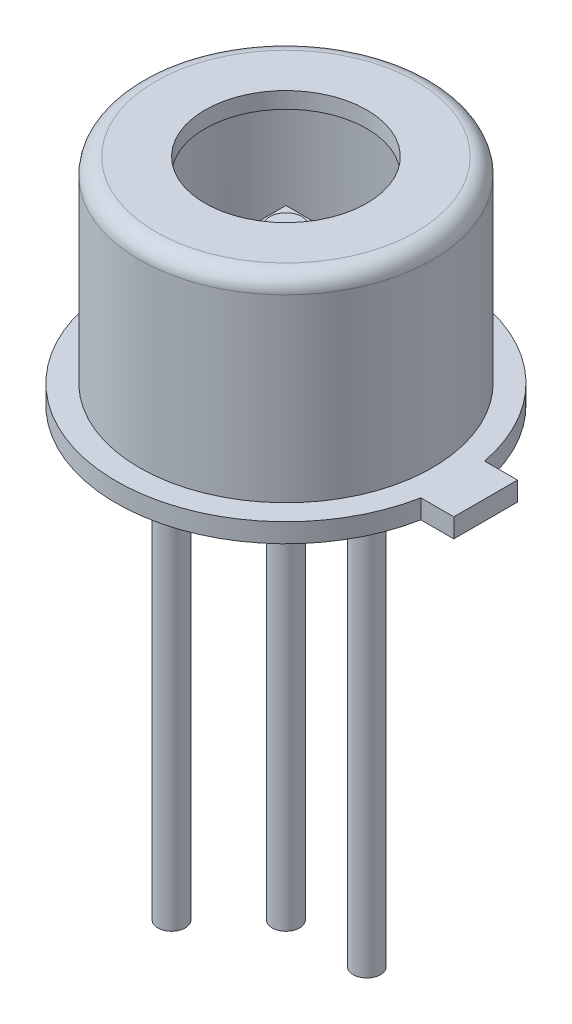
SolidWorks part; units mm, degrees
ref_plane "Front Plane" through (0, 0, 0) normal (0, 0, 1) x (1, 0, 0)
ref_plane "Top Plane" through (0, 0, 0) normal (0, 1, 0) x (1, 0, 0)
ref_plane "Right Plane" through (0, 0, 0) normal (1, 0, 0) x (0, 0, -1)
sketch "Sketch1" plane through (0, 0, 0) normal (0, 0, 1) x (1, 0, 0)
  line L0 (0, 0) -> (0, 37.7864) construction
  line L2 (2.665, 0) -> (2.665, 0.3)
  line L3 (2.665, 0.3) -> (2.3, 0.3)
  line L6 (2.3, 0.3) -> (2.3, 3.126)
  line L7 (2.046, 3.38) -> (1.27, 3.38)
  arc A0 (2.3, 3.126) -> (2.046, 3.38) centre (2.046, 3.126) ccw
  dimension "D7" = 0.254
  dimension "D1" = 0.3
  dimension "D2" = 4.6
  dimension "D4" = 5.33
  dimension "D6" = 3.38
  dimension "D8" = 2.54
revolve "Revolve-Thin2" add sketch "Sketch1" angle 360 about L0
sketch "Sketch2" plane through (0, 0, 0) normal (0, -1, 0) x (1, 0, 0)
  circle A1 centre (0, 0) radius 2.665
  circle A2 centre (0, 0) radius 2.665
  dimension "D1" = 0
extrude "Boss-Extrude1" add sketch "Sketch2" against normal up to surface (0.046 mm away) up to face at (0, 0.046, -2.046)
sketch "Sketch3" plane through (0, 0, 0) normal (0, -1, 0) x (1, 0, 0)
  line L0 (0.375, 0.375) -> (-0.375, -0.375) construction
  line L1 (-0.375, 0.375) -> (0.375, 0.375)
  line L2 (-0.375, 0.375) -> (-0.375, -0.375)
  line L3 (-0.375, -0.375) -> (0.375, -0.375)
  line L4 (0.375, 0.375) -> (0.375, -0.375)
  dimension "D1" = 0.75
extrude "Boss-Extrude2" add sketch "Sketch3" along normal blind 0.05 from offset 2.34 separate body offset against normal yes
sketch "Sketch8" plane through (0, 2.34, 0) normal (0, 1, 0) x (-1, 0, 0)
  circle A0 centre (0, 0) radius 0.25
  dimension "D1" = 0.5
extrude "Boss-Extrude6" add sketch "Sketch8" along normal blind 0.1
sketch "Sketch5" plane through (0, 0, 0) normal (0, -1, 0) x (1, 0, 0)
  line L0 (0, 0) -> (-0.898, 0.898) construction
  line L1 (0, 0) -> (1.27, 0) construction
  circle A0 centre (0, 0) radius 1.27 construction
  circle A1 centre (0, 0) radius 0.215
  circle A2 centre (1.27, 0) radius 0.215
  circle A3 centre (-0.898, 0.898) radius 0.215
  dimension "D1" = 1.27
  dimension "D2" = 0.43
  dimension "D3" = 0.43
  dimension "D4" = 135
  dimension "D5" = 0.43
extrude "Boss-Extrude4" add sketch "Sketch5" along normal blind 7
sketch "Sketch7" plane through (0, 0, 0) normal (0, -1, 0) x (1, 0, 0)
  circle A0 centre (-0.898, 0.898) radius 0.275
  dimension "D1" = 0.55
extrude "Boss-Extrude5" add sketch "Sketch7" along normal blind 0.2
sketch "Sketch10" plane through (0, 0, 0) normal (0, -1, 0) x (1, 0, 0)
  line L0 (0, 0) -> (2.665, 0) construction
  line L2 (3.135, -0.5) -> (2.6177, -0.5)
  line L3 (3.135, -0.5) -> (3.135, 0.5)
  line L4 (3.135, 0.5) -> (2.6177, 0.5)
  line L5 (2.6177, -0.5) -> (2.6177, 0.5)
  line L6 (3.135, -0.5) -> (2.6177, 0.5) construction
  line L7 (3.135, 0.5) -> (2.6177, -0.5) construction
  circle A0 centre (0, 0) radius 2.665 construction
  point P6 (2.8763, 0)
  dimension "D1" = 3.135
  dimension "D2" = 1
extrude "Boss-Extrude7" add sketch "Sketch10" against normal blind 0.3
